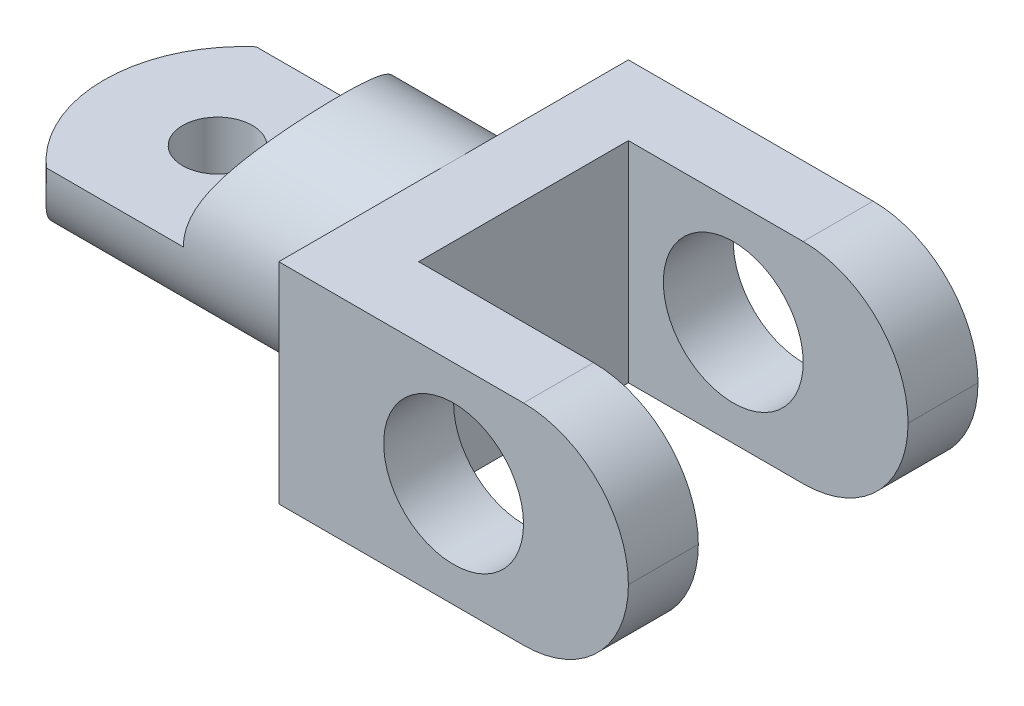
SolidWorks part; units mm, degrees
material "AISI 1035 Steel (SS)"
ref_plane "Front Plane" through (0, 0, 0) normal (0, 0, 1) x (1, 0, 0)
ref_plane "Top Plane" through (0, 0, 0) normal (0, 1, 0) x (1, 0, 0)
ref_plane "Right Plane" through (0, 0, 0) normal (1, 0, 0) x (0, 0, -1)
sketch "Sketch1" plane through (0, 0, 0) normal (0, 1, 0) x (1, 0, 0)
  line L0 (-12.5451, 4.7041) -> (0, 4.7041)
  line L1 (-15.682, 7.841) -> (0, 7.841)
  line L2 (-15.682, 7.841) -> (-15.682, -7.841)
  line L3 (-15.682, -7.841) -> (0, -7.841)
  line L4 (0, 7.841) -> (0, 4.7041)
  line L6 (-12.5451, -4.7041) -> (0, -4.7041)
  line L7 (-12.5451, 4.7041) -> (-12.5451, -4.7041)
  line L8 (-12.5451, 4.7041) -> (-3.1369, 4.7041) construction
  line L9 (-12.5451, -4.7041) -> (-3.1369, -4.7041) construction
  line L10 (0, -4.7041) -> (0, -7.841)
  line L12 (0, 7.841) -> (0, -7.841) construction
  line L13 (-3.1369, 4.7041) -> (-3.1369, -4.7041) construction
  dimension "D1" = 3.1369
extrude "Boss-Extrude1" add sketch "Sketch1" along normal blind 4.7053 and the other way blind 4.7053
sketch "Sketch2" plane through (-15.682, 0, 0) normal (-1, 0, 0) x (0, 0, 1)
  circle A0 centre (0, 0) radius 4.7053
extrude "Boss-Extrude2" add sketch "Sketch2" along normal blind 17.2517
sketch "Sketch3" plane through (0, 4.7053, 0) normal (0, 1, 0) x (1, 0, 0)
  line L0 (0, 4.7041) -> (0, 7.841) construction
  line L1 (-25.0927, 6.2738) -> (-33.6729, 6.2738)
  line L2 (-33.6729, 6.2738) -> (-33.6729, -6.2738)
  line L3 (-33.6729, -6.2738) -> (-25.0927, -6.2738)
  arc A0 (-25.0927, 6.2738) -> (-25.0927, -6.2738) centre (-25.0927, 0) ccw
  dimension "D1" = 25.0927
extrude "Cut-Extrude3" cut sketch "Sketch3" against normal through all
sketch "Sketch5" plane through (0, 4.7053, 0) normal (0, 1, 0) x (1, 0, 0)
  line L0 (0, 4.7041) -> (0, 7.841) construction
  circle A0 centre (-26.6598, 0) radius 5.9009
  dimension "D1" = 26.6598
extrude "Cut-Extrude4" cut sketch "Sketch5" against normal blind 4.7041
sketch "Sketch6" plane through (0, 0.0013, 0) normal (0, 1, 0) x (1, 0, 0)
  line L0 (0, 4.7041) -> (0, 7.841) construction
  circle A0 centre (-26.2687, 0) radius 1.5672
  dimension "D1" = 26.2687
  dimension "D2" = 3.1344
extrude "Cut-Extrude5" cut sketch "Sketch6" against normal through all
fillet "Fillet1" radius 4.7041 4 edges at (0, -4.7053, -6.2725) (0, -4.7053, 6.2725) (0, 4.7053, -6.2725) (0, 4.7053, 6.2725)
sketch "Sketch7" plane through (0, 0, 7.841) normal (0, 0, 1) x (1, 0, 0)
  line L0 (-15.682, -4.7053) -> (-15.682, 4.7053) construction
  circle A0 centre (-7.841, 0) radius 3.1369
  dimension "D1" = 7.841
extrude "Cut-Extrude6" cut sketch "Sketch7" against normal through all
